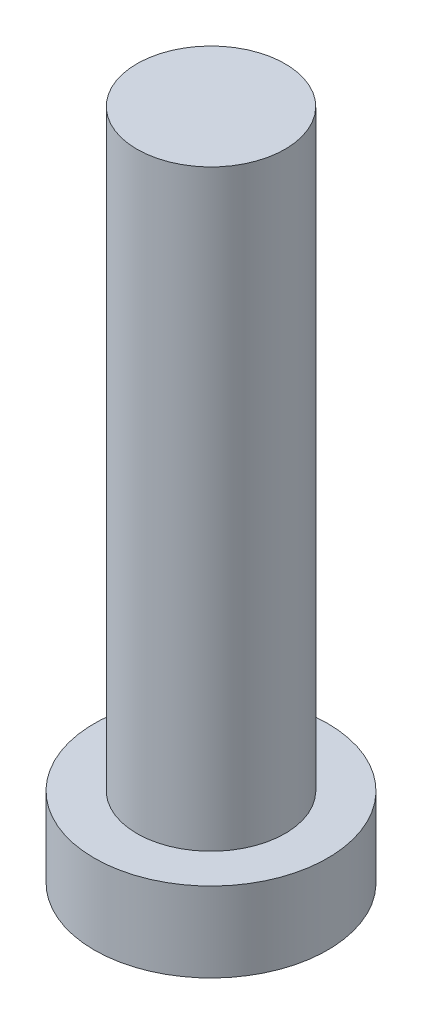
SolidWorks part; units mm, degrees
ref_plane "前视基准面" through (0, 0, 0) normal (0, 0, 1) x (1, 0, 0)
ref_plane "上视基准面" through (0, 0, 0) normal (0, 1, 0) x (1, 0, 0)
ref_plane "右视基准面" through (0, 0, 0) normal (1, 0, 0) x (0, 0, -1)
sketch "草图1" plane through (0, 0, 0) normal (0, 1, 0) x (1, 0, 0)
  circle A0 centre (0, 0) radius 3.15
extrude "凸台-拉伸1" add sketch "草图1" along normal blind 2.15
sketch "草图2" plane through (0, 2.15, 0) normal (0, 1, 0) x (1, 0, 0)
  circle A0 centre (0, 0) radius 2
extrude "凸台-拉伸2" add sketch "草图2" along normal blind 16
sketch "草图3" plane through (0, 0, 0) normal (0, -1, 0) x (1, 0, 0)
  line L0 (-0.5, 1) -> (-0.5, 2)
  line L1 (-2, -0.5) -> (-1, -0.5)
  line L2 (-2, -0.5) -> (-2, 0.5)
  line L3 (-2, 0.5) -> (-1, 0.5)
  line L4 (2, -0.5) -> (2, 0.5)
  line L5 (-2, -0.5) -> (2, 0.5) construction
  line L6 (-2, 0.5) -> (2, -0.5) construction
  line L7 (-0.5, -2) -> (0.5, -2)
  line L8 (-0.5, -2) -> (-0.5, -1)
  line L9 (-0.5, 2) -> (0.5, 2)
  line L10 (0.5, -2) -> (0.5, -1)
  line L11 (-0.5, -2) -> (0.5, 2) construction
  line L12 (-0.5, 2) -> (0.5, -2) construction
  line L13 (1, -0.5) -> (2, -0.5)
  line L14 (0.5, 1) -> (0.5, 2)
  line L15 (1, 0.5) -> (2, 0.5)
  arc A0 (-0.5, -1) -> (-1, -0.5) centre (-1, -1) ccw
  arc A1 (1, -0.5) -> (0.5, -1) centre (1, -1) ccw
  arc A2 (0.5, 1) -> (1, 0.5) centre (1, 1) ccw
  arc A3 (-0.5, 1) -> (-1, 0.5) centre (-1, 1) cw
  point P0 (0, 0)
  point P6 (0, 0)
  point P21 (0.5, 0.5)
  dimension "D1" = 0.5
extrude "切除-拉伸1" cut sketch "草图3" against normal blind 1.5
